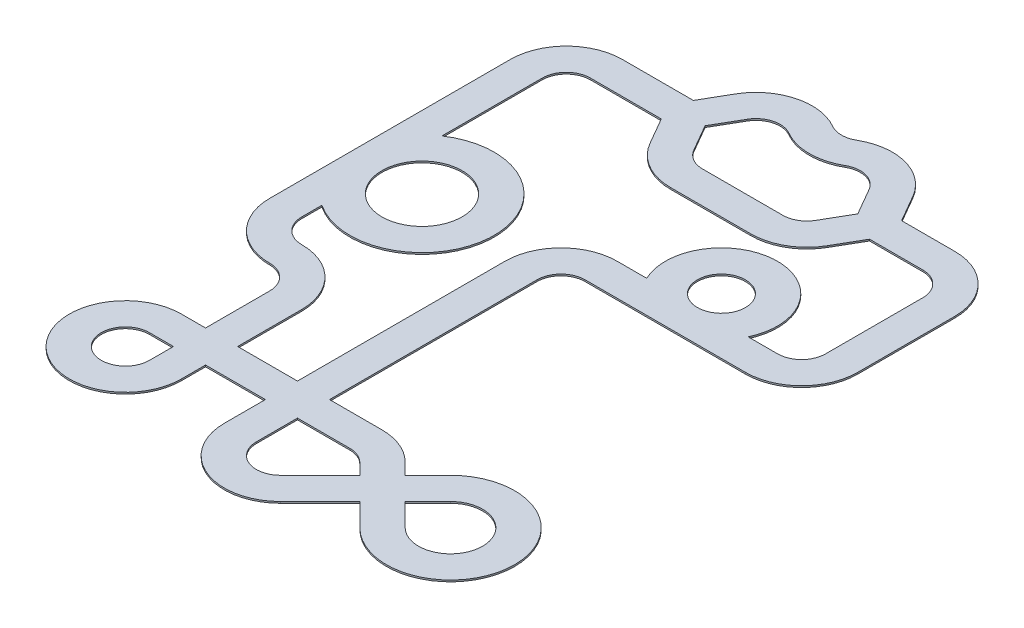
SolidWorks part; units mm, degrees
ref_plane "前视基准面" through (0, 0, 0) normal (0, 0, 1) x (1, 0, 0)
ref_plane "上视基准面" through (0, 0, 0) normal (0, 1, 0) x (1, 0, 0)
ref_plane "右视基准面" through (0, 0, 0) normal (1, 0, 0) x (0, 0, -1)
sketch "草图1" plane through (0, 0, 0) normal (0, 1, 0) x (1, 0, 0)
  line L0 (0, 0) -> (0, -2000) construction
  line L1 (500, 500) -> (1500, 500) construction
  line L2 (1500, 500) -> (1750, 933.0127) construction
  line L3 (1500, 500) -> (1750, 66.9873) construction
  line L4 (2183.0127, -183.0127) -> (3183.0127, -183.0127) construction
  line L5 (3616.0254, 933.0127) -> (3866.0254, 500) construction
  line L6 (3866.0254, 500) -> (4646.4466, 500) construction
  line L7 (3616.0254, 66.9873) -> (3866.0254, 500) construction
  line L8 (5146.4466, 0) -> (5146.4466, -1212.132) construction
  line L9 (4646.4466, -1712.132) -> (3646.4466, -1712.132) construction
  line L10 (3646.4466, -1712.132) -> (2646.4466, -1712.132) construction
  line L11 (2146.4466, -2212.132) -> (2146.4466, -5712.132) construction
  line L12 (3000, -6065.6854) -> (4060.6602, -5005.0253) construction
  line L13 (4060.6602, -5853.5534) -> (3353.5534, -5146.4466) construction
  line L14 (3000, -5000) -> (500, -5000) construction
  line L15 (1000, -5500) -> (1000, -4000) construction
  line L16 (0, -3000) -> (0, -2000) construction
  line L17 (500, 700) -> (1384.5299, 700)
  line L18 (-200, 0) -> (-200, -2000)
  line L19 (1730.9401, 500) -> (1923.2051, 833.0127)
  line L20 (3442.8203, 833.0127) -> (3635.0853, 500)
  line L21 (1384.5299, 300) -> (1576.7949, -33.0127)
  line L22 (2183.0127, -383.0127) -> (3183.0127, -383.0127)
  line L23 (3789.2305, -33.0127) -> (3981.4955, 300)
  line L24 (3981.4955, 300) -> (4646.4466, 300)
  line L25 (4946.4466, 0) -> (4946.4466, -1212.132)
  line L26 (4646.4466, -1512.132) -> (4278.9021, -1512.132)
  line L27 (500, 300) -> (1384.5299, 300)
  line L28 (200, 0) -> (200, -1251.6685)
  line L29 (1384.5299, 700) -> (1576.7949, 1033.0127)
  line L30 (3789.2305, 1033.0127) -> (3981.4955, 700)
  line L31 (1730.9401, 500) -> (1923.2051, 166.9873)
  line L32 (2183.0127, 16.9873) -> (3183.0127, 16.9873)
  line L33 (3442.8203, 166.9873) -> (3635.0853, 500)
  line L34 (3981.4955, 700) -> (4646.4466, 700)
  line L35 (5346.4466, 0) -> (5346.4466, -1212.132)
  line L36 (4646.4466, -1912.132) -> (3646.4466, -1912.132)
  line L37 (4646.4466, -1512.132) -> (3646.4466, -1512.132) construction
  line L38 (1946.4466, -2212.132) -> (1946.4466, -4800)
  line L39 (3141.4214, -6207.1068) -> (3636.3961, -5712.132)
  line L40 (3646.4466, -1912.132) -> (2646.4466, -1912.132)
  line L41 (2346.4466, -2212.132) -> (2346.4466, -4800)
  line L42 (2858.5786, -5924.2641) -> (3353.5534, -5429.2893)
  line L43 (4202.0815, -5712.132) -> (3919.2388, -5429.2893)
  line L44 (3000, -4800) -> (2346.4466, -4800)
  line L45 (3919.2388, -5994.9747) -> (3636.3961, -5712.132)
  line L46 (3000, -5200) -> (2346.4466, -5200)
  line L47 (1200, -5500) -> (1200, -5200)
  line L48 (200, -3000) -> (200, -2748.3315)
  line L49 (800, -5500) -> (800, -5200)
  line L50 (-200, -3000) -> (-200, -2000)
  line L51 (1326.7949, 600) -> (1576.7949, 1033.0127) construction
  line L52 (500, 700) -> (1500, 700) construction
  line L53 (1326.7949, 400) -> (1576.7949, -33.0127) construction
  line L54 (500, 300) -> (1500, 300) construction
  line L55 (1673.2051, 600) -> (1923.2051, 166.9873) construction
  line L56 (1673.2051, 400) -> (1923.2051, 833.0127) construction
  line L57 (3442.8203, 833.0127) -> (3692.8203, 400) construction
  line L58 (3442.8203, 166.9873) -> (3692.8203, 600) construction
  line L59 (3866.0254, 700) -> (4646.4466, 700) construction
  line L60 (3789.2305, 1033.0127) -> (4039.2305, 600) construction
  line L61 (3866.0254, 300) -> (4646.4466, 300) construction
  line L62 (3789.2305, -33.0127) -> (4039.2305, 400) construction
  line L63 (3013.9911, -1512.132) -> (2646.4466, -1512.132)
  line L64 (3646.4466, -1512.132) -> (2646.4466, -1512.132) construction
  line L65 (2346.4466, -5200) -> (2346.4466, -5712.132)
  line L66 (2346.4466, -2212.132) -> (2346.4466, -5712.132) construction
  line L67 (1946.4466, -4800) -> (1200, -4800)
  line L68 (3000, -4800) -> (500, -4800) construction
  line L69 (1946.4466, -5200) -> (1946.4466, -5712.132)
  line L70 (1946.4466, -2212.132) -> (1946.4466, -5712.132) construction
  line L71 (1946.4466, -5200) -> (1200, -5200)
  line L72 (3000, -5200) -> (500, -5200) construction
  line L73 (3636.3961, -5146.4466) -> (3919.2388, -4863.6039)
  line L74 (2858.5786, -5924.2641) -> (3919.2388, -4863.6039) construction
  line L75 (3636.3961, -5146.4466) -> (3494.9747, -5005.0253)
  line L76 (4202.0815, -5712.132) -> (3494.9747, -5005.0253) construction
  line L77 (3919.2388, -5429.2893) -> (4202.0815, -5146.4466)
  line L78 (3141.4214, -6207.1068) -> (4202.0815, -5146.4466) construction
  line L79 (3353.5534, -5429.2893) -> (3212.132, -5287.868)
  line L80 (3919.2388, -5994.9747) -> (3212.132, -5287.868) construction
  line L81 (1200, -4800) -> (1200, -4000)
  line L82 (1200, -5500) -> (1200, -4000) construction
  line L83 (800, -5200) -> (500, -5200)
  line L84 (800, -4800) -> (800, -4000)
  line L85 (800, -5500) -> (800, -4000) construction
  line L86 (800, -4800) -> (500, -4800)
  line L87 (200, 0) -> (200, -2000) construction
  line L88 (200, -3000) -> (200, -2000) construction
  arc A0 (0, 0) -> (500, 500) centre (500, 0) cw construction
  arc A1 (1750, 933.0127) -> (2433.0127, 1116.0254) centre (2183.0127, 683.0127) cw construction
  arc A2 (2433.0127, 1116.0254) -> (2933.0127, 1116.0254) centre (2683.0127, 1549.0381) ccw construction
  arc A3 (2933.0127, 1116.0254) -> (3616.0254, 933.0127) centre (3183.0127, 683.0127) cw construction
  arc A4 (1750, 66.9873) -> (2183.0127, -183.0127) centre (2183.0127, 316.9873) ccw construction
  arc A5 (3183.0127, -183.0127) -> (3616.0254, 66.9873) centre (3183.0127, 316.9873) ccw construction
  arc A6 (4646.4466, 500) -> (5146.4466, 0) centre (4646.4466, 0) cw construction
  arc A7 (5146.4466, -1212.132) -> (4646.4466, -1712.132) centre (4646.4466, -1212.132) cw construction
  arc A8 (3646.4466, -1712.132) -> (3646.4466, -712.132) centre (3646.4466, -1212.132) cw construction
  arc A9 (3646.4466, -712.132) -> (3646.4466, -1712.132) centre (3646.4466, -1212.132) cw construction
  arc A10 (2646.4466, -1712.132) -> (2146.4466, -2212.132) centre (2646.4466, -2212.132) ccw construction
  arc A11 (2146.4466, -5712.132) -> (3000, -6065.6854) centre (2646.4466, -5712.132) ccw construction
  arc A12 (4060.6602, -5005.0253) -> (4060.6602, -5853.5534) centre (4484.9242, -5429.2893) cw construction
  arc A13 (3353.5534, -5146.4466) -> (3000, -5000) centre (3000, -5500) ccw construction
  arc A14 (500, -5000) -> (1000, -5500) centre (500, -5500) ccw construction
  arc A15 (1000, -4000) -> (500, -3500) centre (500, -4000) ccw construction
  arc A16 (500, -3500) -> (0, -3000) centre (500, -3000) cw construction
  arc A17 (0, -2000) -> (1400, -2000) centre (700, -2000) cw construction
  arc A18 (1400, -2000) -> (0, -2000) centre (700, -2000) cw construction
  arc A19 (-200, 0) -> (500, 700) centre (500, 0) cw
  arc A20 (1600, -2000) -> (200, -2748.3315) centre (700, -2000) cw
  arc A21 (1923.2051, 833.0127) -> (2333.0127, 942.8203) centre (2183.0127, 683.0127) cw
  arc A22 (2333.0127, 942.8203) -> (3033.0127, 942.8203) centre (2683.0127, 1549.0381) ccw
  arc A23 (3033.0127, 942.8203) -> (3442.8203, 833.0127) centre (3183.0127, 683.0127) cw
  arc A24 (1576.7949, -33.0127) -> (2183.0127, -383.0127) centre (2183.0127, 316.9873) ccw
  arc A25 (3183.0127, -383.0127) -> (3789.2305, -33.0127) centre (3183.0127, 316.9873) ccw
  arc A26 (4646.4466, 300) -> (4946.4466, 0) centre (4646.4466, 0) cw
  arc A27 (4946.4466, -1212.132) -> (4646.4466, -1512.132) centre (4646.4466, -1212.132) cw
  arc A28 (3646.4466, -1512.132) -> (3646.4466, -912.132) centre (3646.4466, -1212.132) cw
  arc A29 (200, 0) -> (500, 300) centre (500, 0) cw
  arc A30 (1200, -2000) -> (200, -2000) centre (700, -2000) cw
  arc A31 (1576.7949, 1033.0127) -> (2533.0127, 1289.2305) centre (2183.0127, 683.0127) cw
  arc A32 (2533.0127, 1289.2305) -> (2833.0127, 1289.2305) centre (2683.0127, 1549.0381) ccw
  arc A33 (2833.0127, 1289.2305) -> (3789.2305, 1033.0127) centre (3183.0127, 683.0127) cw
  arc A34 (1923.2051, 166.9873) -> (2183.0127, 16.9873) centre (2183.0127, 316.9873) ccw
  arc A35 (3183.0127, 16.9873) -> (3442.8203, 166.9873) centre (3183.0127, 316.9873) ccw
  arc A36 (4646.4466, 700) -> (5346.4466, 0) centre (4646.4466, 0) cw
  arc A37 (5346.4466, -1212.132) -> (4646.4466, -1912.132) centre (4646.4466, -1212.132) cw
  arc A38 (3013.9911, -1512.132) -> (3646.4466, -512.132) centre (3646.4466, -1212.132) cw
  arc A39 (3646.4466, -912.132) -> (3646.4466, -1512.132) centre (3646.4466, -1212.132) cw
  arc A40 (2646.4466, -1512.132) -> (1946.4466, -2212.132) centre (2646.4466, -2212.132) ccw
  arc A41 (1946.4466, -5712.132) -> (3141.4214, -6207.1068) centre (2646.4466, -5712.132) ccw
  arc A42 (4202.0815, -5146.4466) -> (4202.0815, -5712.132) centre (4484.9242, -5429.2893) cw
  arc A43 (3646.4466, -512.132) -> (4278.9021, -1512.132) centre (3646.4466, -1212.132) cw
  arc A44 (2646.4466, -1912.132) -> (2346.4466, -2212.132) centre (2646.4466, -2212.132) ccw
  arc A45 (2346.4466, -5712.132) -> (2858.5786, -5924.2641) centre (2646.4466, -5712.132) ccw
  arc A46 (3919.2388, -4863.6039) -> (3919.2388, -5994.9747) centre (4484.9242, -5429.2893) cw
  arc A47 (3494.9747, -5005.0253) -> (3000, -4800) centre (3000, -5500) ccw
  arc A48 (500, -4800) -> (1200, -5500) centre (500, -5500) ccw
  arc A49 (3212.132, -5287.868) -> (3000, -5200) centre (3000, -5500) ccw
  arc A50 (500, -5200) -> (800, -5500) centre (500, -5500) ccw
  arc A51 (1200, -4000) -> (500, -3300) centre (500, -4000) ccw
  arc A52 (500, -3300) -> (200, -3000) centre (500, -3000) cw
  arc A53 (200, -2000) -> (1200, -2000) centre (700, -2000) cw
  arc A54 (800, -4000) -> (500, -3700) centre (500, -4000) ccw
  arc A55 (500, -3700) -> (-200, -3000) centre (500, -3000) cw
  arc A57 (3646.4466, -512.132) -> (3646.4466, -1912.132) centre (3646.4466, -1212.132) cw construction
  arc A58 (3646.4466, -1912.132) -> (3646.4466, -512.132) centre (3646.4466, -1212.132) cw construction
  arc A60 (1600, -2000) -> (-200, -2000) centre (700, -2000) cw construction
  arc A61 (200, -1251.6685) -> (1600, -2000) centre (700, -2000) cw
  arc A62 (-200, -2000) -> (1600, -2000) centre (700, -2000) cw construction
  dimension "D2" = 500
  dimension "D4" = 500
  dimension "D5" = 500
  dimension "D6" = 500
  dimension "D8" = 90
  dimension "D10" = 500
  dimension "D11" = 500
  dimension "D15" = 500
  dimension "D16" = 500
  dimension "D17" = 500
  dimension "D18" = 1000
  dimension "D20" = 500
  dimension "D21" = 500
  dimension "D22" = 600
  dimension "D25" = 500
  dimension "D26" = 500
  dimension "D27" = 500
  dimension "D29" = 700
  dimension "D30" = 2000
  dimension "D34" = 500
  dimension "D38" = 1000
  dimension "D1" = 120
  dimension "D3" = 120
  dimension "D7" = 60
  dimension "D9" = 90
  dimension "D12" = 60
  dimension "D13" = 60
  dimension "D14" = 500
  dimension "D19" = 1000
  dimension "D23" = 225
  dimension "D24" = 90
  dimension "D28" = 90
  dimension "D31" = 1000
  dimension "D32" = 1500
  dimension "D33" = 2500
  dimension "D35" = 1000
  dimension "D36" = 1500
  dimension "D37" = 3500
  dimension "D39" = 200
  dimension "D40" = 200
  dimension "D41" = 200
  dimension "D42" = 200
  dimension "D43" = 200
  dimension "D44" = 200
  dimension "D45" = 200
  dimension "D46" = 200
extrude "凸台-拉伸1" add sketch "草图1" along normal blind 20 contours A55 A54 L84 L86 A48 L47 L71 L69 A41 L39 L45 A46 L73 L75 A47 L44 L41 A44 L40 L36 A37 L35 A36 L34 L30 A33 A32 A31 L29 L17 A19 L18 L50 A61 L28 A29 L27 L21 A24 L22 A25 L23 L24 A26 L25 A27 L26 A43 A38 L63
